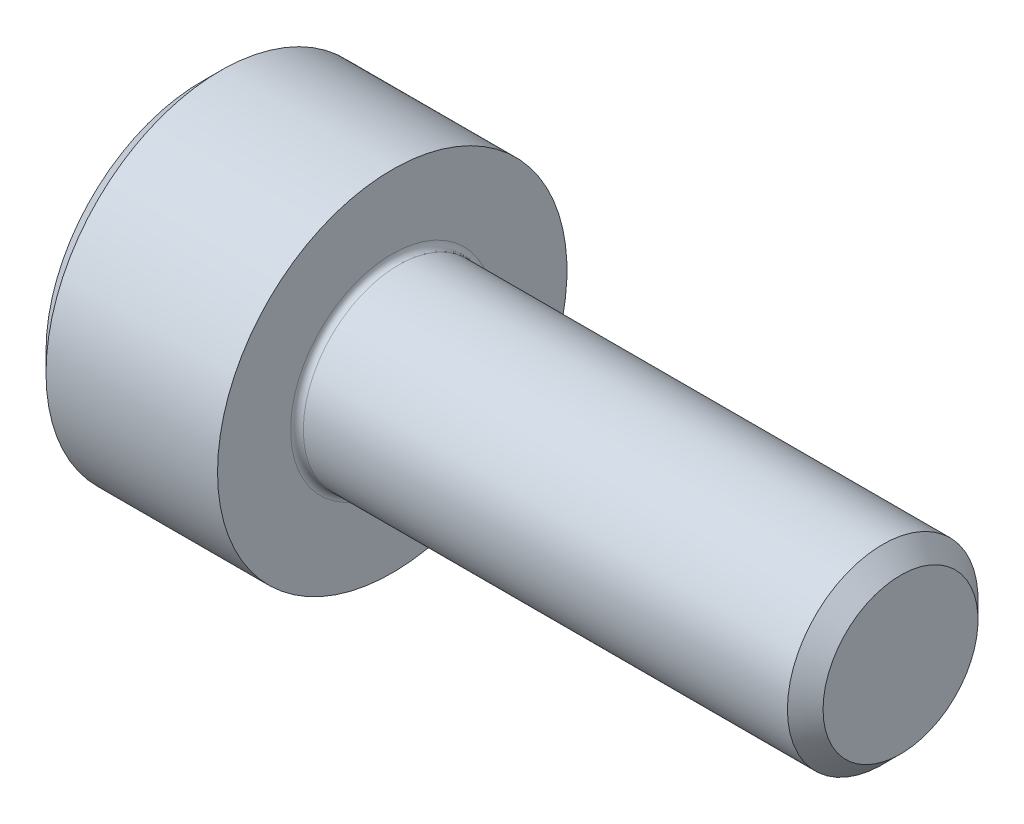
SolidWorks part; units mm, degrees
revolve "Base-Revolve" add sketch "BodySke"
sketch "BodySke" plane through (0, 0, 0) normal (0, 0, 1) x (1, 0, 0)
  line L0 (0, 0) -> (0, 2.45)
  line L1 (0.3, 2.75) -> (3, 2.75)
  line L2 (3, 2.75) -> (3, 1.5)
  line L3 (3, 1.5) -> (10.7195, 1.5)
  line L4 (11, 1.2195) -> (11, 0)
  line L5 (11, 0) -> (0, 0)
  line L6 (-31.75, 0) -> (127, 0) construction
  line L7 (0, 2.45) -> (0.3, 2.75)
  line L8 (11, 1.2195) -> (10.7195, 1.5)
  line L9 (0, -2.45) -> (0.3, -2.75) construction
  line L10 (11, -1.2195) -> (10.7195, -1.5) construction
  line L11 (3.5, 9.525) -> (3.5, 3.175) construction
  line L12 (3, 9.525) -> (3, 3.175) construction
  line L13 (-39, 9.525) -> (-39, 3.175) construction
  dimension "Diameter" = 3
  dimension "Head_ht" = 3
  dimension "Length" = 8
  dimension "Body_ch_ang" = 45
  dimension "Head_dia" = 5.5
  dimension "Head_ch_ang" = 45
  dimension "Minor_dia" = 2.439
  dimension "Advance" = 0.5
  dimension "Thread_nom" = 8
  dimension "Thread_length" = 50
  dimension "Head_ch_ht" = 0.3
cosmetic thread "ThreadCosmetic"
fillet "Fillet1" radius 0.1 1 edges at (3, 0, 1.5)
ref_plane "Plane1" through (0, 0, 0) normal (0, 0, 1) x (1, 0, 0)
ref_plane "Plane2" through (0, 0, 0) normal (0, 1, 0) x (1, 0, 0)
ref_plane "Plane3" through (0, 0, 0) normal (1, 0, 0) x (0, 0, -1)
sketch "Sketch2" plane through (0, 0, 0) normal (0, 0, 1) x (1, 0, 0)
  line L0 (0, 1.28) -> (1.3, 1.28)
  line L1 (1.3, 1.28) -> (2.039, 0)
  line L2 (-31.75, 0) -> (127, 0) construction
  line L3 (2.039, 0) -> (0, 0)
  line L4 (0, 0) -> (0, 1.28)
  line L5 (0, 2.45) -> (0, -2.45) construction
  line L6 (0, 0) -> (47.625, 0) construction
  line L7 (3, -2.75) -> (3, 2.75) construction
  dimension "D1" = 1.28
  dimension "D2" = 60
revolve "Hex-PreBroach" cut sketch "Sketch2" angle 360 about L6
sketch "Sketch3" plane through (0, 0, 0) normal (-1, 0, 0) x (0, 0.5, 0.866)
  line L0 (0.739, 1.28) -> (-0.739, 1.28)
  line L1 (-0.739, 1.28) -> (-1.478, 0)
  line L2 (0.739, 1.28) -> (1.478, 0)
  line L3 (0.739, -1.28) -> (1.478, 0)
  line L4 (0.739, -1.28) -> (-0.739, -1.28)
  line L5 (-0.739, -1.28) -> (-1.478, 0)
  dimension "D1" = 1.28
  dimension "D2" = 1.28
  dimension "Hex_size" = 2.56
extrude "Hex" cut sketch "Sketch3" against normal blind 1.3
sketch "Sketch4" plane through (0, 0, 0) normal (-1, 0, 0) x (0, 0, 1)
  line L0 (0, 0) -> (1.4605, 0)
  line L1 (0, 0) -> (6.1484, 3.5498) construction
  line L2 (0, 0) -> (0.7302, 1.2648)
  line L3 (1.2009, 0.3267) -> (1.3933, 0.4378)
  line L4 (0.8834, 0.8767) -> (1.0758, 0.9877)
  arc A0 (1.2009, 0.3267) -> (0.8834, 0.8767) centre (0, 0) ccw
  arc A1 (1.4605, 0) -> (1.3933, 0.4378) centre (0, 0) ccw
  arc A2 (0.7302, 1.2648) -> (1.0758, 0.9877) centre (0, 0) cw
  dimension "D1" = 30
  dimension "D2" = 60
  dimension "Spline_p_dim" = 0.635
  dimension "D3" = 0.3175
extrude "Spline" [suppressed] cut sketch "Sketch4" against normal blind 1.3
pattern_circular "CirPattern1" [suppressed] count 6 every 60
sketch "Sketch5" plane through (0, 0, 0) normal (0, 0, 1) x (1, 0, 0)
  line L0 (-31.75, 0) -> (127, 0) construction
  line L2 (0, 2.45) -> (0, -2.45) construction
  circle A0 centre (1.2, 0) radius 0.475
  dimension "Drilled_hole_dia" = 0.95
  dimension "Drilled_hole_loc" = 1.2
extrude "Hole" [suppressed] cut sketch "Sketch5" against normal through all and the other way through all
pattern_circular "Drilled-4" [suppressed] count 2 every 60
pattern_circular "Drilled-6" [suppressed] count 3 every 60
sketch "ThdSchSke" plane through (0, 0, 0) normal (0, 0, 1) x (1, 0, 0)
  line L0 (3.5, -1.2195) -> (3.3036, -1.5)
  line L1 (3.5, -1.2195) -> (3.6964, -1.5)
  line L2 (3.6964, -1.5) -> (3.6964, -1.875)
  line L3 (-3.175, 0) -> (5.1513, 0) construction
  line L5 (3.6964, -1.875) -> (3.3036, -1.875)
  line L6 (3.3036, -1.875) -> (3.3036, -1.5)
  line L7 (0, 2.45) -> (0, -2.45) construction
  dimension "Thread_minor" = 2.439
  dimension "Diameter" = 3
  dimension "Start" = 3.5
revolve "ThreadSchematic" [suppressed] cut sketch "ThdSchSke" angle 360 about L3
pattern_linear "ThdSchPat" [suppressed]
equation "\"D2@Sketch3\" = \"Hex_size@Sketch3\" / 2"
equation "\"D1@Sketch3\" = \"Hex_size@Sketch3\" / 2"
equation "\"D1@Sketch2\" = \"Hex_size@Sketch3\" / 2"
equation "\"D3@Sketch4\" = \"Spline_p_dim@Sketch4\" / 2"
equation "\"Thread_minor@ThreadCosmetic\"  =  \"Minor_dia@BodySke\""
equation "\"D2@CirPattern1\" = 360 / \"Num_teeth@CirPattern1\""
equation "\"Wall_thickness@Sketch2\" = \"Head_ht@BodySke\" - \"Key_eng@Hex\""
equation "\"Thread_length@ThreadCosmetic\" = ((sgn( (\"Length@BodySke\" - \"Advance@BodySke\" ) - \"Thread_nom@BodySke\" )-1)*( (\"Length@BodySke\" - \"Advance@BodySke\" ) - \"Thread_nom@BodySke\" ))/-2+ \"Thread_nom@BodySke\""
equation "\"Thread_minor@ThdSchSke\" = \"Minor_dia@BodySke\""
equation "\"Diameter@ThdSchSke\" = \"Diameter@BodySke\""
equation "\"Overcut@ThdSchSke\" = \"Diameter@BodySke\" * 1.25"
equation "\"Start@ThdSchSke\" = \"Head_ht@BodySke\" + \"Length@BodySke\" - \"Thread_length@ThreadCosmetic\"  '---Non-countersunk---"
equation "\"Num_threads@ThdSchPat\" = int( \"Thread_length@ThreadCosmetic\" / \"Advance@BodySke\" + 0.999 )  + 1"
equation "\"Advance@ThdSchPat\" = \"Thread_length@ThreadCosmetic\" /  (\"Num_threads@ThdSchPat\" - 1) 'relax it"
equation "\"Num_threads@ThdSchPat\" = \"Num_threads@ThdSchPat\" - sgn( \"Num_threads@ThdSchPat\" - 1) '---chamfered tips only---"
